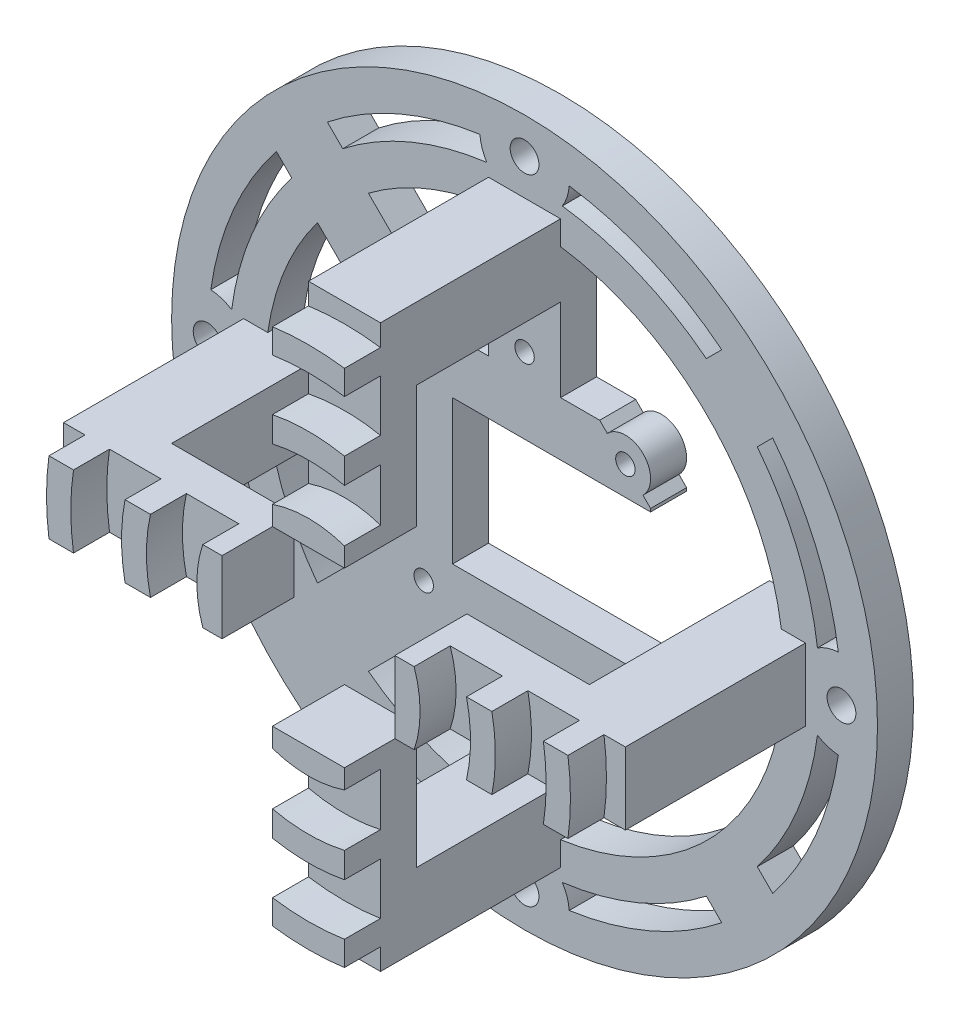
SolidWorks part; units mm, degrees
other "Markup1"
sketch "Sketch33" plane through (-49, -49, 0) normal (0, 0, -1) x (-1, 0, 0)
ref_plane "Front Plane" through (0, 0, 0) normal (0, 0, 1) x (1, 0, 0)
ref_plane "Top Plane" through (0, 0, 0) normal (0, 1, 0) x (1, 0, 0)
ref_plane "Right Plane" through (0, 0, 0) normal (1, 0, 0) x (0, 0, -1)
sketch "Sketch1" plane through (0, 0, 0) normal (0, 0, 1) x (1, 0, 0)
  circle A1 centre (0, 0) radius 49
  dimension "D1" = 98
extrude "Boss-Extrude1" add sketch "Sketch1" along normal blind 5
sketch "Sketch23" plane through (0, 0, 5) normal (0, 0, 1) x (1, 0, 0)
  line L5 (10.4289, -17.5) -> (5, -17.5)
  line L6 (17.5, -10.4289) -> (17.5, -5)
  line L7 (10.4289, 17.5) -> (5, 17.5)
  line L8 (-17.5, -10.4289) -> (-17.5, -5)
  line L9 (-5, -17.5) -> (-10.4289, -17.5)
  line L10 (10.4289, -17.5) -> (27.3756, -34.4467)
  line L15 (-27.3756, -34.4467) -> (-10.4289, -17.5)
  line L28 (5, -40.313) -> (5, -17.5)
  line L30 (-5, -40.313) -> (-5, -17.5)
  line L32 (-17.5, 5) -> (-17.5, 10.4289)
  line L34 (-34.4467, -27.3756) -> (-17.5, -10.4289)
  line L36 (-40.313, -5) -> (-17.5, -5)
  line L38 (-40.313, 5) -> (-17.5, 5)
  line L40 (-34.4467, 27.3756) -> (-17.5, 10.4289)
  line L42 (-27.3756, 34.4467) -> (-10.4289, 17.5)
  line L45 (-5, 17.5) -> (-10.4289, 17.5)
  line L50 (17.5, -5) -> (40.313, -5)
  line L51 (17.5, 5) -> (17.5, 10.4289)
  line L52 (17.5, 10.4289) -> (34.4467, 27.3756)
  line L58 (-5, 17.5) -> (-5, 40.313)
  line L62 (17.5, -10.4289) -> (34.4467, -27.3756)
  line L66 (5, 17.5) -> (5, 40.313)
  line L67 (10.4289, 17.5) -> (27.3756, 34.4467)
  line L68 (17.5, 5) -> (40.313, 5)
  arc A0 (-34.4467, 27.3756) -> (-43.5614, 6.1969) centre (0, 0) ccw
  arc A1 (-27.3756, -34.4467) -> (-6.1969, -43.5614) centre (0, 0) ccw
  arc A2 (-6.1969, 43.5614) -> (-5, 40.313) centre (0, 44) ccw
  arc A3 (40.313, -5) -> (43.5614, -6.1969) centre (44, 0) ccw
  arc A4 (6.1969, -43.5614) -> (5, -40.313) centre (0, -44) ccw
  arc A5 (-40.313, 5) -> (-43.5614, 6.1969) centre (-44, 0) ccw
  arc A6 (6.1969, -43.5614) -> (27.3756, -34.4467) centre (0, 0) ccw
  arc A7 (34.4467, -27.3756) -> (43.5614, -6.1969) centre (0, 0) ccw
  arc A8 (43.5614, 6.1969) -> (34.4467, 27.3756) centre (0, 0) ccw
  arc A9 (-43.5614, -6.1969) -> (-34.4467, -27.3756) centre (0, 0) ccw
  arc A10 (43.5614, 6.1969) -> (40.313, 5) centre (44, 0) ccw
  arc A11 (-43.5614, -6.1969) -> (-40.313, -5) centre (-44, 0) ccw
  arc A12 (-6.1969, 43.5614) -> (-27.3756, 34.4467) centre (0, 0) ccw
  arc A13 (-5, -40.313) -> (-6.1969, -43.5614) centre (0, -44) ccw
  arc A14 (5, 40.313) -> (6.1969, 43.5614) centre (0, 44) ccw
  arc A15 (27.3756, 34.4467) -> (6.1969, 43.5614) centre (0, 0) ccw
  point P14 (0, 0)
  dimension "D1" = 4
  dimension "D2" = 88
  dimension "D8" = 12.4248
  dimension "D6" = 4
extrude "Cut-Extrude11" cut sketch "Sketch23" against normal through all contours A5 L38 L32 L40 A0 | A11 A9 L34 L8 L36 | A13 L30 L9 L15 A1 | A4 A6 L10 L5 L28 | A10 A8 L52 L51 L68 | L67 A15 A14 L66 L7 | A2 A12 L42 L45 L58 | L62 A7 A3 L50 L6
sketch "Sketch24" plane through (0, 0, 5) normal (0, 0, 1) x (1, 0, 0)
  line L1 (14, -14) -> (-14, -14)
  line L2 (14, -14) -> (14, 14)
  line L3 (14, 14) -> (-14, 14)
  line L4 (-14, -14) -> (-14, 14)
  line L5 (14, -14) -> (-14, 14) construction
  line L6 (14, 14) -> (-14, -14) construction
  circle A0 centre (-14, 14) radius 1.35
  circle A1 centre (14, 14) radius 1.35
  circle A2 centre (14, -14) radius 1.35
  circle A3 centre (-14, -14) radius 1.35
  point P0 (0, 0)
  dimension "D1" = 28
  dimension "D2" = 28
extrude "Cut-Extrude12" cut sketch "Sketch24" against normal through all contours A0 | A1 | A2 | A3
sketch "Sketch25" plane through (0, 0, 5) normal (0, 0, 1) x (1, 0, 0)
  circle A0 centre (0, 44) radius 2
extrude "Cut-Extrude13" cut sketch "Sketch25" against normal through all
pattern_circular "CirPattern6" count 4 over 360 about axis through (0, 0, 0) along (0, 0, 1) of "Cut-Extrude13"
sketch "Sketch26" plane through (0, 0, 5) normal (0, 0, 1) x (1, 0, 0)
  line L0 (-5, 17.5) -> (-5, 40.313) construction
  line L9 (5, 29) -> (-5, 29)
  line L10 (5, 29) -> (5, 39)
  line L11 (5, 39) -> (-5, 39)
  line L12 (-5, 29) -> (-5, 39)
  line L13 (5, 29) -> (-5, 39) construction
  line L14 (5, 39) -> (-5, 29) construction
  circle A0 centre (0, 44) radius 2 construction
  point P0 (0, 34)
  dimension "D1" = 10
  dimension "D2" = 10
  dimension "D3" = 10
extrude "Boss-Extrude23" add sketch "Sketch26" along normal blind 20
pattern_circular "CirPattern7" count 4 over 360 about axis through (0, 0, 0) along (0, 0, 1) of "Boss-Extrude23"
sketch "Sketch28" plane through (0, 0, 25) normal (0, 0, 1) x (1, 0, 0)
  line L0 (-5, 39) -> (-5, 12)
  line L1 (5, 39) -> (5, 12)
  line L2 (5, 12) -> (-5, 12)
  line L3 (5, 39) -> (-5, 39)
  dimension "D1" = 27
extrude "Boss-Extrude25" add sketch "Sketch28" along normal blind 5
pattern_circular "CirPattern9" count 4 over 360 about axis through (0, 0, 0) along (0, 0, 1) of "Boss-Extrude25"
sketch "Sketch29" plane through (0, 0, 30) normal (0, 0, 1) x (1, 0, 0)
  line L0 (5, 12) -> (-5, 12)
  line L1 (-5, 12) -> (5, 12) construction
  line L2 (-5, 39) -> (-5, 12)
  line L3 (5, 39) -> (5, 12)
  arc A0 (5, 14.6714) -> (-5, 14.6714) centre (0, 0) ccw
  arc A1 (5, 21.9374) -> (-5, 21.9374) centre (0, 0) ccw
  arc A3 (5, 25.4637) -> (-5, 25.4637) centre (0, 0) ccw
  arc A4 (5, 32.619) -> (-5, 32.619) centre (0, 0) ccw
  arc A6 (5, 36.0247) -> (-5, 36.0247) centre (0, 0) ccw
  dimension "D1" = 31
  dimension "D2" = 45
  dimension "D3" = 66
  dimension "D4" = 51.9
  dimension "D5" = 72.74
extrude "Boss-Extrude26" add sketch "Sketch29" along normal blind 5 contours L3 A6 L2 A4 | L3 A3 L2 A1 | L3 A0 L2 L0
pattern_circular "CirPattern10" count 4 over 360 about axis through (0, 0, 0) along (0, 0, 1) of "Boss-Extrude26"
sketch "Sketch30" plane through (0, 0, 0) normal (0, 0, -1) x (-1, 0, 0)
  circle A0 centre (0, 0) radius 41
  circle A1 centre (0, 0) radius 36
  dimension "D1" = 82
  dimension "D2" = 72
extrude "Boss-Extrude27" add sketch "Sketch30" against normal up to surface (5 mm away) up to face at (-44, 2, 5)
sketch "Sketch31" plane through (0, 0, 0) normal (0, 0, -1) x (-1, 0, 0)
  line L0 (-5, 35.6511) -> (-5, 17.5)
  line L1 (-5, 17.5) -> (-10.4289, 17.5)
  line L6 (-5, -17.5) -> (-5, -35.6511)
  line L21 (-5, -17.5) -> (-10.4289, -17.5)
  line L22 (-10.4289, -17.5) -> (-11.5004, -16.4499)
  line L23 (-17.5, -10.4289) -> (-16.4499, -11.5004)
  line L24 (-10.4289, 17.5) -> (-11.4898, 16.4391)
  line L25 (-17.5, 10.4289) -> (-17.5, -10.4289)
  line L26 (-16.4391, 11.4898) -> (-17.5, 10.4289)
  line L27 (-35.6511, 5) -> (-29.0011, 5)
  line L28 (-17.5, 5) -> (-35.6511, 5) construction
  line L29 (-29.0011, 5) -> (-29.0011, -5)
  line L30 (-17.5, -5) -> (-35.6511, -5) construction
  line L31 (-29.0011, -5) -> (-35.6511, -5)
  arc A2 (-5, 35.6511) -> (-35.6511, 5) centre (0, 0) ccw
  arc A3 (-21.6736, -28.7447) -> (-5, -35.6511) centre (0, 0) ccw construction
  arc A4 (-35.6511, -5) -> (-5, -35.6511) centre (0, 0) ccw
  arc A6 (-16.4499, -11.5004) -> (-11.5004, -16.4499) centre (-14, -14) ccw
  arc A7 (-11.4898, 16.4391) -> (-16.4391, 11.4898) centre (-14, 14) ccw
  dimension "D1" = 6.65
extrude "Cut-Extrude14" cut sketch "Sketch31" against normal up to surface (5 mm away) up to face at (16.3507, 38.42, 5)
sketch "Sketch32" plane through (0, 0, 0) normal (0, 0, -1) x (-1, 0, 0)
  line L0 (-10, 10) -> (-17.5, 10)
  line L1 (-10, -10) -> (10, -10)
  line L2 (-10, -10) -> (-10, 10)
  line L3 (-10, 10) -> (10, 10)
  line L4 (10, -10) -> (10, 10)
  line L5 (-10, -10) -> (10, 10) construction
  line L6 (-10, 10) -> (10, -10) construction
  line L7 (-17.5, -10.4289) -> (-17.5, 10.4289) construction
  line L8 (-17.5, 10) -> (-17.5, -10)
  line L9 (-17.5, -10) -> (-10, -10)
  point P0 (0, 0)
  dimension "D1" = 20
extrude "Cut-Extrude15" cut sketch "Sketch32" against normal up to surface (5 mm away) contours L1 L4 L3 L2 | L8 L9 L2 L0 up to face at (6.6008, -0.0003, 5)
sketch "Sketch34" plane through (0, 0, 0) normal (0, 0, -1) x (-1, 0, 0)
  circle A0 centre (0, 20.5) radius 1.35
  circle A1 centre (0, 35.5) radius 1.35
  dimension "D1" = 2.7
  dimension "D2" = 2.7
  dimension "D3" = 15
  dimension "D4" = 20.5
extrude "Cut-Extrude16" cut sketch "Sketch34" against normal up to surface (5 mm away) up to face at (16.3507, 38.42, 5)
pattern_circular "CirPattern11" count 2 over 90 about axis through (0, 0, 0) along (0, 0, 1) of "Cut-Extrude16"
